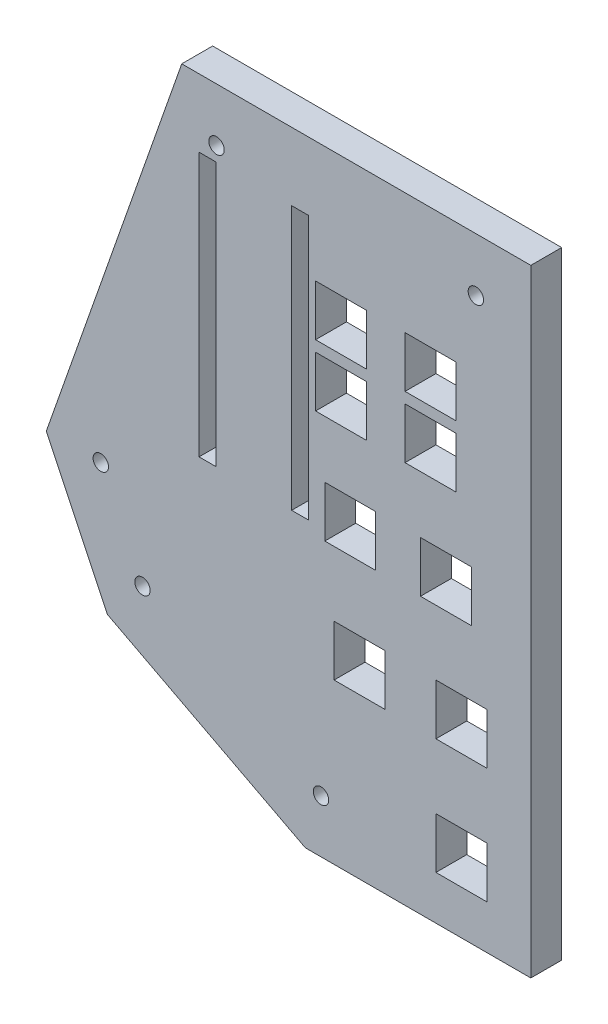
SolidWorks part; units mm, degrees
ref_plane "Front Plane" through (0, 0, 0) normal (0, 0, 1) x (1, 0, 0)
ref_plane "Top Plane" through (0, 0, 0) normal (0, 1, 0) x (1, 0, 0)
ref_plane "Right Plane" through (0, 0, 0) normal (1, 0, 0) x (0, 0, -1)
sketch "Sketch1" plane through (0, 0, 0) normal (0, 0, 1) x (1, 0, 0)
  line L6 (-20.066, -57.15) -> (46.99, -57.15) construction
  line L7 (-12.446, -73.152) -> (46.99, -73.152) construction
  line L8 (-4.1204, 6.35) -> (53.34, 6.35)
  line L9 (53.34, 6.35) -> (53.34, -95.25)
  line L10 (53.34, -95.25) -> (16.225, -95.25)
  line L16 (-4.1204, 6.35) -> (-26.416, -57.15)
  line L18 (-20.066, -57.15) -> (-26.416, -57.15) construction
  line L26 (0, 0) -> (46.99, 0) construction
  line L27 (46.99, 0) -> (46.99, -88.9) construction
  line L28 (46.99, -88.9) -> (17.78, -88.9) construction
  line L29 (17.78, -88.9) -> (-12.446, -73.152) construction
  line L30 (-12.446, -73.152) -> (-20.066, -57.15) construction
  line L31 (-20.066, -57.15) -> (0, 0) construction
  line L32 (46.99, -57.15) -> (46.99, -88.9) construction
  line L33 (17.78, -88.9) -> (16.225, -95.25) construction
  line L34 (-12.446, -73.152) -> (-17.9301, -78.4424) construction
  line L35 (16.225, -95.25) -> (-16.3566, -78.2747)
  line L36 (-26.416, -57.15) -> (-16.3566, -78.2747)
  point P40 (24.6098, 6.35)
  dimension "D1" = 88.9
  dimension "D2" = 29.21
  dimension "D3" = 59.436
  dimension "D4" = 67.056
  dimension "D5" = 6.35
  dimension "D6" = 6.35
  dimension "D7" = 46.99
  dimension "D8" = 6.35
  dimension "D13" = 103.76
  dimension "D14" = 6.35
  dimension "D17" = 108.51
  dimension "D22" = 5.7332
extrude "Boss-Extrude1" add sketch "Sketch1" along normal blind 5.08
sketch "Sketch3" plane through (0, 0, 5.08) normal (0, 0, 1) x (1, 0, 0)
  line L0 (46.99, -88.9) -> (0, -88.9) construction
  line L6 (-20.066, -57.15) -> (46.99, -57.15) construction
  line L7 (-12.446, -73.152) -> (46.99, -73.152) construction
  line L8 (0, 0) -> (46.99, 0) construction
  line L9 (46.99, 0) -> (46.99, -88.9) construction
  line L10 (46.99, -88.9) -> (17.78, -88.9) construction
  line L11 (17.78, -88.9) -> (-12.446, -73.152) construction
  line L12 (-12.446, -73.152) -> (-20.066, -57.15) construction
  line L13 (-20.066, -57.15) -> (0, 0) construction
sketch "Sketch5" plane through (0, 0, 0) normal (0, 0, -1) x (-1, 0, 0)
  line L0 (-46.99, 0) -> (-46.99, -17.78) construction
  line L1 (-46.99, 0) -> (-1.524, 0) construction
  line L2 (-46.99, -17.78) -> (-36.83, -17.78) construction
  line L3 (-46.99, 0) -> (-46.99, -27.94) construction
  line L8 (-41.021, -13.589) -> (-32.639, -13.589)
  line L9 (-41.021, -13.589) -> (-41.021, -21.971)
  line L10 (-46.99, 0) -> (-46.99, -45.72) construction
  line L15 (-41.021, -21.971) -> (-32.639, -21.971)
  line L16 (-32.639, -13.589) -> (-32.639, -21.971)
  line L17 (-46.99, 0) -> (-46.99, -88.9) construction
  line L18 (-46.99, -45.72) -> (-39.37, -45.72) construction
  line L19 (-41.021, -13.589) -> (-32.639, -21.971) construction
  line L20 (-46.99, 0) -> (-46.99, -64.77) construction
  line L21 (-43.561, -41.529) -> (-35.179, -41.529)
  line L22 (-43.561, -41.529) -> (-43.561, -49.911)
  line L23 (-43.561, -49.911) -> (-35.179, -49.911)
  line L24 (-35.179, -41.529) -> (-35.179, -49.911)
  line L25 (-43.561, -41.529) -> (-35.179, -49.911) construction
  line L26 (-43.561, -49.911) -> (-35.179, -41.529) construction
  line L27 (-46.99, -64.77) -> (-41.91, -64.77) construction
  line L28 (-41.021, -21.971) -> (-32.639, -13.589) construction
  line L29 (-46.99, -27.94) -> (-36.83, -27.94) construction
  line L30 (-46.99, 0) -> (-46.99, -83.82) construction
  line L31 (-41.021, -23.749) -> (-32.639, -23.749)
  line L32 (-41.021, -23.749) -> (-41.021, -32.131)
  line L33 (-41.021, -32.131) -> (-32.639, -32.131)
  line L34 (-32.639, -23.749) -> (-32.639, -32.131)
  line L35 (-41.021, -23.749) -> (-32.639, -32.131) construction
  line L36 (-41.021, -32.131) -> (-32.639, -23.749) construction
  line L37 (-46.101, -60.579) -> (-37.719, -60.579)
  line L38 (-46.101, -60.579) -> (-46.101, -68.961)
  line L39 (-46.101, -68.961) -> (-37.719, -68.961)
  line L40 (-37.719, -60.579) -> (-37.719, -68.961)
  line L41 (-46.101, -60.579) -> (-37.719, -68.961) construction
  line L42 (-46.101, -68.961) -> (-37.719, -60.579) construction
  line L43 (-46.99, -83.82) -> (-41.91, -83.82) construction
  line L44 (-36.83, -17.78) -> (-22.098, -17.78) construction
  line L45 (-46.101, -79.629) -> (-37.719, -79.629)
  line L46 (-46.101, -79.629) -> (-46.101, -88.011)
  line L47 (-46.101, -88.011) -> (-37.719, -88.011)
  line L48 (-37.719, -79.629) -> (-37.719, -88.011)
  line L49 (-46.101, -79.629) -> (-37.719, -88.011) construction
  line L50 (-46.101, -88.011) -> (-37.719, -79.629) construction
  line L51 (-36.83, -27.94) -> (-22.098, -27.94) construction
  line L52 (-39.37, -45.72) -> (-23.622, -45.72) construction
  line L53 (-41.91, -64.77) -> (-25.146, -64.77) construction
  line L54 (-46.99, 0) -> (-16.764, 0) construction
  line L55 (-26.289, -13.589) -> (-17.907, -13.589)
  line L56 (-26.289, -13.589) -> (-26.289, -21.971)
  line L57 (-26.289, -21.971) -> (-17.907, -21.971)
  line L58 (-17.907, -13.589) -> (-17.907, -21.971)
  line L59 (-26.289, -13.589) -> (-17.907, -21.971) construction
  line L60 (-26.289, -21.971) -> (-17.907, -13.589) construction
  line L61 (-26.289, -23.749) -> (-17.907, -23.749)
  line L62 (-26.289, -23.749) -> (-26.289, -32.131)
  line L63 (-26.289, -32.131) -> (-17.907, -32.131)
  line L64 (-17.907, -23.749) -> (-17.907, -32.131)
  line L65 (-26.289, -23.749) -> (-17.907, -32.131) construction
  line L66 (-26.289, -32.131) -> (-17.907, -23.749) construction
  line L67 (-27.813, -41.529) -> (-19.431, -41.529)
  line L68 (-27.813, -41.529) -> (-27.813, -49.911)
  line L69 (-27.813, -49.911) -> (-19.431, -49.911)
  line L70 (-19.431, -41.529) -> (-19.431, -49.911)
  line L71 (-27.813, -41.529) -> (-19.431, -49.911) construction
  line L72 (-27.813, -49.911) -> (-19.431, -41.529) construction
  line L73 (-29.337, -60.579) -> (-20.955, -60.579)
  line L74 (-29.337, -60.579) -> (-29.337, -68.961)
  line L75 (-29.337, -68.961) -> (-20.955, -68.961)
  line L76 (-20.955, -60.579) -> (-20.955, -68.961)
  line L77 (-29.337, -60.579) -> (-20.955, -68.961) construction
  line L78 (-29.337, -68.961) -> (-20.955, -60.579) construction
  line L79 (0, 0) -> (-46.99, 0) construction
  line L80 (-16.764, 0) -> (-16.764, -4.826) construction
  line L81 (-46.99, 0) -> (-13.97, 0) construction
  line L82 (-13.97, 0) -> (-13.97, -4.826) construction
  line L83 (-1.524, 0) -> (-1.524, -4.826) construction
  line L84 (-46.99, 0) -> (-17.1256, 0) construction
  line L85 (-1.524, 0) -> (-1.524, -48.26) construction
  line L86 (-46.99, 0) -> (1.27, 0) construction
  line L87 (1.27, 0) -> (1.27, -4.826) construction
  line L88 (-16.764, 0) -> (-16.764, -48.26) construction
  line L90 (-16.764, -4.826) -> (-13.97, -4.826)
  line L91 (-16.764, -4.826) -> (-16.764, -48.26)
  line L92 (-16.764, -48.26) -> (-13.97, -48.26)
  line L93 (-13.97, -4.826) -> (-13.97, -48.26)
  line L94 (-1.524, -4.826) -> (1.27, -4.826)
  line L95 (-1.524, -4.826) -> (-1.524, -48.26)
  line L96 (-1.524, -48.26) -> (1.27, -48.26)
  line L97 (1.27, -4.826) -> (1.27, -48.26)
  dimension "D2" = 8.382
  dimension "D3" = 64.77
  dimension "D4" = 8.382
  dimension "D5" = 10.16
  dimension "D6" = 17.78
  dimension "D7" = 8.382
  dimension "D8" = 8.382
  dimension "D9" = 45.72
  dimension "D10" = 7.62
  dimension "D11" = 8.382
  dimension "D12" = 8.382
  dimension "D13" = 27.94
  dimension "D14" = 10.16
  dimension "D15" = 5.08
  dimension "D16" = 8.382
  dimension "D17" = 8.382
  dimension "D18" = 8.382
  dimension "D19" = 8.382
  dimension "D20" = 83.82
  dimension "D21" = 5.08
  dimension "D22" = 8.382
  dimension "D23" = 8.382
  dimension "D24" = 14.732
  dimension "D25" = 8.382
  dimension "D26" = 8.382
  dimension "D27" = 14.732
  dimension "D28" = 8.382
  dimension "D29" = 8.382
  dimension "D30" = 15.748
  dimension "D31" = 8.382
  dimension "D32" = 8.382
  dimension "D33" = 16.764
  dimension "D34" = 30.226
  dimension "D35" = 4.826
  dimension "D36" = 33.02
  dimension "D37" = 4.826
  dimension "D38" = 45.466
  dimension "D39" = 4.826
  dimension "D40" = 48.26
  dimension "D41" = 4.826
  dimension "D42" = 48.26
  dimension "D43" = 48.26
extrude "Cut-Extrude1" cut sketch "Sketch5" against normal through all
sketch "Sketch7" plane through (0, 0, 5.08) normal (0, 0, 1) x (1, 0, 0)
  line L0 (46.99, 0) -> (44.2976, 0) construction
  line L1 (0, 0) -> (46.99, 0) construction
  line L2 (44.2976, 0) -> (44.2976, -2.4892) construction
  line L3 (46.99, 0) -> (1.6002, 0) construction
  line L4 (1.6002, 0) -> (1.6002, -2.4384) construction
  line L5 (-20.066, -57.15) -> (-17.4498, -57.15) construction
  line L6 (-20.066, -57.15) -> (46.99, -57.15) construction
  line L7 (-12.446, -73.152) -> (-10.5918, -73.152) construction
  line L8 (-12.446, -73.152) -> (46.99, -73.152) construction
  line L9 (-10.5918, -73.152) -> (-10.5918, -71.3486) construction
  line L10 (17.78, -88.9) -> (17.78, -86.5378) construction
  line L11 (17.78, -86.5378) -> (18.796, -86.5378) construction
  circle A0 centre (44.2976, -2.4892) radius 1.27
  circle A1 centre (1.6002, -2.4384) radius 1.27
  circle A2 centre (-17.4498, -57.15) radius 1.27
  circle A3 centre (-10.5918, -71.3486) radius 1.27
  circle A4 centre (18.796, -86.5378) radius 1.27
  dimension "D3" = 2.54
  dimension "D6" = 2.54
  dimension "D8" = 2.54
  dimension "D11" = 2.54
  dimension "D14" = 2.54
  dimension "D1" = 2.6924
  dimension "D2" = 2.4892
  dimension "D4" = 45.3898
  dimension "D5" = 2.4384
  dimension "D7" = 2.6162
  dimension "D9" = 1.8542
  dimension "D10" = 1.8034
  dimension "D12" = 2.3622
  dimension "D13" = 1.016
extrude "Cut-Extrude3" cut sketch "Sketch7" against normal through all
